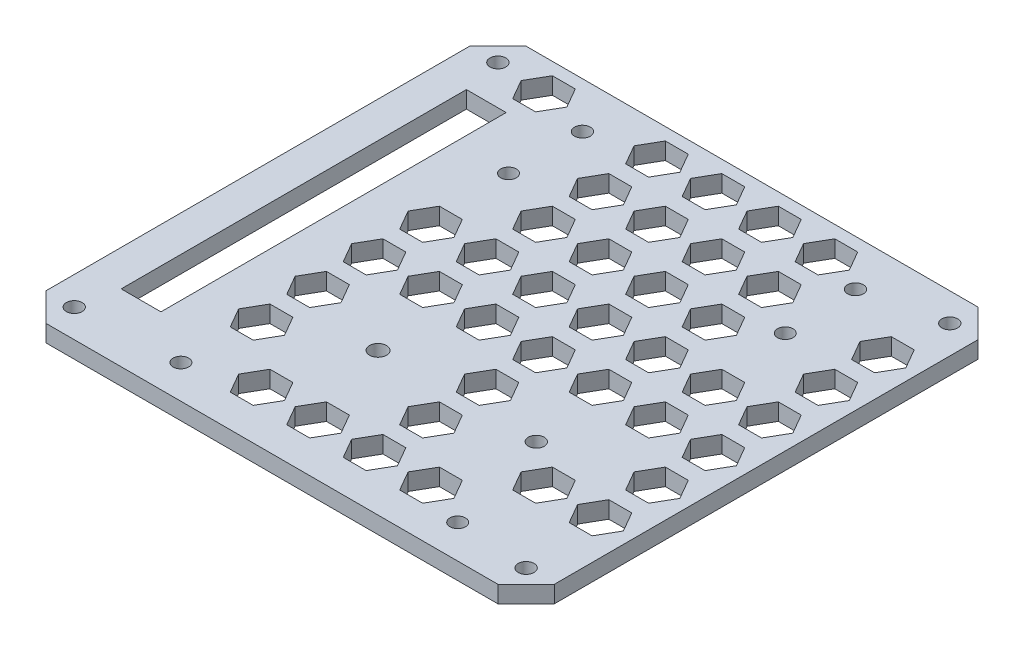
SolidWorks part; units mm, degrees
ref_plane "Front Plane" through (0, 0, 0) normal (0, 0, 1) x (1, 0, 0)
ref_plane "Top Plane" through (0, 0, 0) normal (0, 1, 0) x (1, 0, 0)
ref_plane "Right Plane" through (0, 0, 0) normal (1, 0, 0) x (0, 0, -1)
sketch "Sketch1" plane through (0, 0, 0) normal (0, 1, 0) x (1, 0, 0)
  line L0 (-40, 37.5) -> (40, 37.5) construction
  line L1 (40, 37.5) -> (40, -37.5) construction
  line L2 (40, -37.5) -> (-40, -37.5) construction
  line L3 (-40, -37.5) -> (-40, 37.5) construction
  line L4 (-40, 37.5) -> (-40, 42.5) construction
  line L5 (-40, 37.5) -> (-45, 37.5) construction
  line L6 (40, -37.5) -> (45, -37.5) construction
  line L7 (40, -37.5) -> (40, -42.5) construction
  line L8 (-45, 42.5) -> (-45, -42.5)
  line L9 (-45, -42.5) -> (45, -42.5)
  line L10 (45, -42.5) -> (45, 42.5)
  line L11 (45, 42.5) -> (-45, 42.5)
  circle A0 centre (-40, 37.5) radius 1.4
  circle A1 centre (40, 37.5) radius 1.4
  circle A2 centre (40, -37.5) radius 1.4
  circle A3 centre (-40, -37.5) radius 1.4
extrude "Boss-Extrude1" add sketch "Sketch1" along normal blind 3
sketch "Sketch4" plane through (0, 3, 0) normal (0, 1, 0) x (1, 0, 0)
  circle A0 centre (26.9483, -36.5641) radius 1.375
  circle A1 centre (-22.0517, -36.5641) radius 1.375
  circle A2 centre (-22.0517, 21.4359) radius 1.375
  circle A3 centre (26.9483, 21.4359) radius 1.375
extrude "Cut-Extrude1" cut sketch "Sketch4" against normal blind 10
sketch "Sketch5" plane through (0, 0, 0) normal (0, -1, 0) x (-1, 0, 0)
  circle A0 centre (6.4695, -17.2479) radius 1.5
  circle A1 centre (-21.5467, -17.2479) radius 1.4
  circle A2 centre (-26.4252, 34.3776) radius 1.4
  circle A3 centre (21.911, 34.3776) radius 1.4
extrude "Cut-Extrude2" cut sketch "Sketch5" against normal blind 10 contours A3 | A2 | A0 | A1
sketch "Sketch6" plane through (0, 3, 0) normal (0, 1, 0) x (1, 0, 0)
  line L1 (-31.5917, -30.5577) -> (-38.6326, -30.5577)
  line L2 (-31.5917, -30.5577) -> (-31.5917, 30.5577)
  line L3 (-31.5917, 30.5577) -> (-38.6326, 30.5577)
  line L4 (-38.6326, -30.5577) -> (-38.6326, 30.5577)
  line L5 (-31.5917, -30.5577) -> (-38.6326, 30.5577) construction
  line L6 (-31.5917, 30.5577) -> (-38.6326, -30.5577) construction
  point P0 (-35.1122, 0)
extrude "Cut-Extrude3" cut sketch "Sketch6" against normal blind 10
chamfer "Chamfer1" distance 5 angle 45 4 edges at (-45, 1.5, 42.5) (45, 1.5, 42.5) (45, 1.5, -42.5) (-45, 1.5, -42.5)
sketch "Sketch7" plane through (0, 3, 0) normal (0, 1, 0) x (1, 0, 0)
  line L0 (40, 42.5) -> (-40, 42.5) construction
  line L1 (-29.0872, 33.2663) -> (-27.0592, 36.7789)
  line L2 (-27.0592, 36.7789) -> (-29.0872, 40.2914)
  line L3 (-29.0872, 40.2914) -> (-33.1431, 40.2914)
  line L4 (-33.1431, 40.2914) -> (-35.1711, 36.7789)
  line L5 (-35.1711, 36.7789) -> (-33.1431, 33.2663)
  line L6 (-33.1431, 33.2663) -> (-29.0872, 33.2663)
  line L7 (-19.0872, 33.2663) -> (-17.0592, 36.7789) [skipped]
  line L8 (-17.0592, 36.7789) -> (-19.0872, 40.2914) [skipped]
  line L9 (-19.0872, 40.2914) -> (-23.1431, 40.2914) [skipped]
  line L10 (-23.1431, 40.2914) -> (-25.1711, 36.7789) [skipped]
  line L11 (-25.1711, 36.7789) -> (-23.1431, 33.2663) [skipped]
  line L12 (-23.1431, 33.2663) -> (-19.0872, 33.2663) [skipped]
  line L13 (-9.0872, 33.2663) -> (-7.0592, 36.7789)
  line L14 (-7.0592, 36.7789) -> (-9.0872, 40.2914)
  line L15 (-9.0872, 40.2914) -> (-13.1431, 40.2914)
  line L16 (-13.1431, 40.2914) -> (-15.1711, 36.7789)
  line L17 (-15.1711, 36.7789) -> (-13.1431, 33.2663)
  line L18 (-13.1431, 33.2663) -> (-9.0872, 33.2663)
  line L19 (0.9128, 33.2663) -> (2.9408, 36.7789)
  line L20 (2.9408, 36.7789) -> (0.9128, 40.2914)
  line L21 (0.9128, 40.2914) -> (-3.1431, 40.2914)
  line L22 (-3.1431, 40.2914) -> (-5.1711, 36.7789)
  line L23 (-5.1711, 36.7789) -> (-3.1431, 33.2663)
  line L24 (-3.1431, 33.2663) -> (0.9128, 33.2663)
  line L25 (10.9128, 33.2663) -> (12.9408, 36.7789)
  line L26 (12.9408, 36.7789) -> (10.9128, 40.2914)
  line L27 (10.9128, 40.2914) -> (6.8569, 40.2914)
  line L28 (6.8569, 40.2914) -> (4.8289, 36.7789)
  line L29 (4.8289, 36.7789) -> (6.8569, 33.2663)
  line L30 (6.8569, 33.2663) -> (10.9128, 33.2663)
  line L31 (20.9128, 33.2663) -> (22.9408, 36.7789)
  line L32 (22.9408, 36.7789) -> (20.9128, 40.2914)
  line L33 (20.9128, 40.2914) -> (16.8569, 40.2914)
  line L34 (16.8569, 40.2914) -> (14.8289, 36.7789)
  line L35 (14.8289, 36.7789) -> (16.8569, 33.2663)
  line L36 (16.8569, 33.2663) -> (20.9128, 33.2663)
  line L37 (30.9128, 33.2663) -> (32.9408, 36.7789) [skipped]
  line L38 (32.9408, 36.7789) -> (30.9128, 40.2914) [skipped]
  line L39 (30.9128, 40.2914) -> (26.8569, 40.2914) [skipped]
  line L40 (26.8569, 40.2914) -> (24.8289, 36.7789) [skipped]
  line L41 (24.8289, 36.7789) -> (26.8569, 33.2663) [skipped]
  line L42 (26.8569, 33.2663) -> (30.9128, 33.2663) [skipped]
  line L43 (40.9128, 33.2663) -> (42.9408, 36.7789) [skipped]
  line L44 (42.9408, 36.7789) -> (40.9128, 40.2914) [skipped]
  line L45 (40.9128, 40.2914) -> (36.8569, 40.2914) [skipped]
  line L46 (36.8569, 40.2914) -> (34.8289, 36.7789) [skipped]
  line L47 (34.8289, 36.7789) -> (36.8569, 33.2663) [skipped]
  line L48 (36.8569, 33.2663) -> (40.9128, 33.2663) [skipped]
  line L49 (-19.0872, 23.2663) -> (-17.0592, 26.7789) [skipped]
  line L50 (-17.0592, 26.7789) -> (-19.0872, 30.2914) [skipped]
  line L51 (-19.0872, 30.2914) -> (-23.1431, 30.2914) [skipped]
  line L52 (-23.1431, 30.2914) -> (-25.1711, 26.7789) [skipped]
  line L53 (-25.1711, 26.7789) -> (-23.1431, 23.2663) [skipped]
  line L54 (-23.1431, 23.2663) -> (-19.0872, 23.2663) [skipped]
  line L55 (-9.0872, 23.2663) -> (-7.0592, 26.7789)
  line L56 (-7.0592, 26.7789) -> (-9.0872, 30.2914)
  line L57 (-9.0872, 30.2914) -> (-13.1431, 30.2914)
  line L58 (-13.1431, 30.2914) -> (-15.1711, 26.7789)
  line L59 (-15.1711, 26.7789) -> (-13.1431, 23.2663)
  line L60 (-13.1431, 23.2663) -> (-9.0872, 23.2663)
  line L61 (0.9128, 23.2663) -> (2.9408, 26.7789)
  line L62 (2.9408, 26.7789) -> (0.9128, 30.2914)
  line L63 (0.9128, 30.2914) -> (-3.1431, 30.2914)
  line L64 (-3.1431, 30.2914) -> (-5.1711, 26.7789)
  line L65 (-5.1711, 26.7789) -> (-3.1431, 23.2663)
  line L66 (-3.1431, 23.2663) -> (0.9128, 23.2663)
  line L67 (10.9128, 23.2663) -> (12.9408, 26.7789)
  line L68 (12.9408, 26.7789) -> (10.9128, 30.2914)
  line L69 (10.9128, 30.2914) -> (6.8569, 30.2914)
  line L70 (6.8569, 30.2914) -> (4.8289, 26.7789)
  line L71 (4.8289, 26.7789) -> (6.8569, 23.2663)
  line L72 (6.8569, 23.2663) -> (10.9128, 23.2663)
  line L73 (20.9128, 23.2663) -> (22.9408, 26.7789)
  line L74 (22.9408, 26.7789) -> (20.9128, 30.2914)
  line L75 (20.9128, 30.2914) -> (16.8569, 30.2914)
  line L76 (16.8569, 30.2914) -> (14.8289, 26.7789)
  line L77 (14.8289, 26.7789) -> (16.8569, 23.2663)
  line L78 (16.8569, 23.2663) -> (20.9128, 23.2663)
  line L79 (30.9128, 23.2663) -> (32.9408, 26.7789) [skipped]
  line L80 (32.9408, 26.7789) -> (30.9128, 30.2914) [skipped]
  line L81 (30.9128, 30.2914) -> (26.8569, 30.2914) [skipped]
  line L82 (26.8569, 30.2914) -> (24.8289, 26.7789) [skipped]
  line L83 (24.8289, 26.7789) -> (26.8569, 23.2663) [skipped]
  line L84 (26.8569, 23.2663) -> (30.9128, 23.2663) [skipped]
  line L85 (40.9128, 23.2663) -> (42.9408, 26.7789)
  line L86 (42.9408, 26.7789) -> (40.9128, 30.2914)
  line L87 (40.9128, 30.2914) -> (36.8569, 30.2914)
  line L88 (36.8569, 30.2914) -> (34.8289, 26.7789)
  line L89 (34.8289, 26.7789) -> (36.8569, 23.2663)
  line L90 (36.8569, 23.2663) -> (40.9128, 23.2663)
  line L91 (-19.0872, 13.2663) -> (-17.0592, 16.7789) [skipped]
  line L92 (-17.0592, 16.7789) -> (-19.0872, 20.2914) [skipped]
  line L93 (-19.0872, 20.2914) -> (-23.1431, 20.2914) [skipped]
  line L94 (-23.1431, 20.2914) -> (-25.1711, 16.7789) [skipped]
  line L95 (-25.1711, 16.7789) -> (-23.1431, 13.2663) [skipped]
  line L96 (-23.1431, 13.2663) -> (-19.0872, 13.2663) [skipped]
  line L97 (-9.0872, 13.2663) -> (-7.0592, 16.7789)
  line L98 (-7.0592, 16.7789) -> (-9.0872, 20.2914)
  line L99 (-9.0872, 20.2914) -> (-13.1431, 20.2914)
  line L100 (-13.1431, 20.2914) -> (-15.1711, 16.7789)
  line L101 (-15.1711, 16.7789) -> (-13.1431, 13.2663)
  line L102 (-13.1431, 13.2663) -> (-9.0872, 13.2663)
  line L103 (0.9128, 13.2663) -> (2.9408, 16.7789)
  line L104 (2.9408, 16.7789) -> (0.9128, 20.2914)
  line L105 (0.9128, 20.2914) -> (-3.1431, 20.2914)
  line L106 (-3.1431, 20.2914) -> (-5.1711, 16.7789)
  line L107 (-5.1711, 16.7789) -> (-3.1431, 13.2663)
  line L108 (-3.1431, 13.2663) -> (0.9128, 13.2663)
  line L109 (10.9128, 13.2663) -> (12.9408, 16.7789)
  line L110 (12.9408, 16.7789) -> (10.9128, 20.2914)
  line L111 (10.9128, 20.2914) -> (6.8569, 20.2914)
  line L112 (6.8569, 20.2914) -> (4.8289, 16.7789)
  line L113 (4.8289, 16.7789) -> (6.8569, 13.2663)
  line L114 (6.8569, 13.2663) -> (10.9128, 13.2663)
  line L115 (20.9128, 13.2663) -> (22.9408, 16.7789)
  line L116 (22.9408, 16.7789) -> (20.9128, 20.2914)
  line L117 (20.9128, 20.2914) -> (16.8569, 20.2914)
  line L118 (16.8569, 20.2914) -> (14.8289, 16.7789)
  line L119 (14.8289, 16.7789) -> (16.8569, 13.2663)
  line L120 (16.8569, 13.2663) -> (20.9128, 13.2663)
  line L121 (30.9128, 13.2663) -> (32.9408, 16.7789) [skipped]
  line L122 (32.9408, 16.7789) -> (30.9128, 20.2914) [skipped]
  line L123 (30.9128, 20.2914) -> (26.8569, 20.2914) [skipped]
  line L124 (26.8569, 20.2914) -> (24.8289, 16.7789) [skipped]
  line L125 (24.8289, 16.7789) -> (26.8569, 13.2663) [skipped]
  line L126 (26.8569, 13.2663) -> (30.9128, 13.2663) [skipped]
  line L127 (40.9128, 13.2663) -> (42.9408, 16.7789)
  line L128 (42.9408, 16.7789) -> (40.9128, 20.2914)
  line L129 (40.9128, 20.2914) -> (36.8569, 20.2914)
  line L130 (36.8569, 20.2914) -> (34.8289, 16.7789)
  line L131 (34.8289, 16.7789) -> (36.8569, 13.2663)
  line L132 (36.8569, 13.2663) -> (40.9128, 13.2663)
  line L133 (-19.0872, 3.2663) -> (-17.0592, 6.7789)
  line L134 (-17.0592, 6.7789) -> (-19.0872, 10.2914)
  line L135 (-19.0872, 10.2914) -> (-23.1431, 10.2914)
  line L136 (-23.1431, 10.2914) -> (-25.1711, 6.7789)
  line L137 (-25.1711, 6.7789) -> (-23.1431, 3.2663)
  line L138 (-23.1431, 3.2663) -> (-19.0872, 3.2663)
  line L139 (-9.0872, 3.2663) -> (-7.0592, 6.7789)
  line L140 (-7.0592, 6.7789) -> (-9.0872, 10.2914)
  line L141 (-9.0872, 10.2914) -> (-13.1431, 10.2914)
  line L142 (-13.1431, 10.2914) -> (-15.1711, 6.7789)
  line L143 (-15.1711, 6.7789) -> (-13.1431, 3.2663)
  line L144 (-13.1431, 3.2663) -> (-9.0872, 3.2663)
  line L145 (0.9128, 3.2663) -> (2.9408, 6.7789)
  line L146 (2.9408, 6.7789) -> (0.9128, 10.2914)
  line L147 (0.9128, 10.2914) -> (-3.1431, 10.2914)
  line L148 (-3.1431, 10.2914) -> (-5.1711, 6.7789)
  line L149 (-5.1711, 6.7789) -> (-3.1431, 3.2663)
  line L150 (-3.1431, 3.2663) -> (0.9128, 3.2663)
  line L151 (10.9128, 3.2663) -> (12.9408, 6.7789)
  line L152 (12.9408, 6.7789) -> (10.9128, 10.2914)
  line L153 (10.9128, 10.2914) -> (6.8569, 10.2914)
  line L154 (6.8569, 10.2914) -> (4.8289, 6.7789)
  line L155 (4.8289, 6.7789) -> (6.8569, 3.2663)
  line L156 (6.8569, 3.2663) -> (10.9128, 3.2663)
  line L157 (20.9128, 3.2663) -> (22.9408, 6.7789)
  line L158 (22.9408, 6.7789) -> (20.9128, 10.2914)
  line L159 (20.9128, 10.2914) -> (16.8569, 10.2914)
  line L160 (16.8569, 10.2914) -> (14.8289, 6.7789)
  line L161 (14.8289, 6.7789) -> (16.8569, 3.2663)
  line L162 (16.8569, 3.2663) -> (20.9128, 3.2663)
  line L163 (30.9128, 3.2663) -> (32.9408, 6.7789)
  line L164 (32.9408, 6.7789) -> (30.9128, 10.2914)
  line L165 (30.9128, 10.2914) -> (26.8569, 10.2914)
  line L166 (26.8569, 10.2914) -> (24.8289, 6.7789)
  line L167 (24.8289, 6.7789) -> (26.8569, 3.2663)
  line L168 (26.8569, 3.2663) -> (30.9128, 3.2663)
  line L169 (40.9128, 3.2663) -> (42.9408, 6.7789)
  line L170 (42.9408, 6.7789) -> (40.9128, 10.2914)
  line L171 (40.9128, 10.2914) -> (36.8569, 10.2914)
  line L172 (36.8569, 10.2914) -> (34.8289, 6.7789)
  line L173 (34.8289, 6.7789) -> (36.8569, 3.2663)
  line L174 (36.8569, 3.2663) -> (40.9128, 3.2663)
  line L175 (-19.0872, -6.7337) -> (-17.0592, -3.2211)
  line L176 (-17.0592, -3.2211) -> (-19.0872, 0.2914)
  line L177 (-19.0872, 0.2914) -> (-23.1431, 0.2914)
  line L178 (-23.1431, 0.2914) -> (-25.1711, -3.2211)
  line L179 (-25.1711, -3.2211) -> (-23.1431, -6.7337)
  line L180 (-23.1431, -6.7337) -> (-19.0872, -6.7337)
  line L181 (-9.0872, -6.7337) -> (-7.0592, -3.2211)
  line L182 (-7.0592, -3.2211) -> (-9.0872, 0.2914)
  line L183 (-9.0872, 0.2914) -> (-13.1431, 0.2914)
  line L184 (-13.1431, 0.2914) -> (-15.1711, -3.2211)
  line L185 (-15.1711, -3.2211) -> (-13.1431, -6.7337)
  line L186 (-13.1431, -6.7337) -> (-9.0872, -6.7337)
  line L187 (0.9128, -6.7337) -> (2.9408, -3.2211)
  line L188 (2.9408, -3.2211) -> (0.9128, 0.2914)
  line L189 (0.9128, 0.2914) -> (-3.1431, 0.2914)
  line L190 (-3.1431, 0.2914) -> (-5.1711, -3.2211)
  line L191 (-5.1711, -3.2211) -> (-3.1431, -6.7337)
  line L192 (-3.1431, -6.7337) -> (0.9128, -6.7337)
  line L193 (10.9128, -6.7337) -> (12.9408, -3.2211)
  line L194 (12.9408, -3.2211) -> (10.9128, 0.2914)
  line L195 (10.9128, 0.2914) -> (6.8569, 0.2914)
  line L196 (6.8569, 0.2914) -> (4.8289, -3.2211)
  line L197 (4.8289, -3.2211) -> (6.8569, -6.7337)
  line L198 (6.8569, -6.7337) -> (10.9128, -6.7337)
  line L199 (20.9128, -6.7337) -> (22.9408, -3.2211)
  line L200 (22.9408, -3.2211) -> (20.9128, 0.2914)
  line L201 (20.9128, 0.2914) -> (16.8569, 0.2914)
  line L202 (16.8569, 0.2914) -> (14.8289, -3.2211)
  line L203 (14.8289, -3.2211) -> (16.8569, -6.7337)
  line L204 (16.8569, -6.7337) -> (20.9128, -6.7337)
  line L205 (30.9128, -6.7337) -> (32.9408, -3.2211)
  line L206 (32.9408, -3.2211) -> (30.9128, 0.2914)
  line L207 (30.9128, 0.2914) -> (26.8569, 0.2914)
  line L208 (26.8569, 0.2914) -> (24.8289, -3.2211)
  line L209 (24.8289, -3.2211) -> (26.8569, -6.7337)
  line L210 (26.8569, -6.7337) -> (30.9128, -6.7337)
  line L211 (40.9128, -6.7337) -> (42.9408, -3.2211)
  line L212 (42.9408, -3.2211) -> (40.9128, 0.2914)
  line L213 (40.9128, 0.2914) -> (36.8569, 0.2914)
  line L214 (36.8569, 0.2914) -> (34.8289, -3.2211)
  line L215 (34.8289, -3.2211) -> (36.8569, -6.7337)
  line L216 (36.8569, -6.7337) -> (40.9128, -6.7337)
  line L217 (-19.0872, -16.7337) -> (-17.0592, -13.2211)
  line L218 (-17.0592, -13.2211) -> (-19.0872, -9.7086)
  line L219 (-19.0872, -9.7086) -> (-23.1431, -9.7086)
  line L220 (-23.1431, -9.7086) -> (-25.1711, -13.2211)
  line L221 (-25.1711, -13.2211) -> (-23.1431, -16.7337)
  line L222 (-23.1431, -16.7337) -> (-19.0872, -16.7337)
  line L223 (-9.0872, -16.7337) -> (-7.0592, -13.2211) [skipped]
  line L224 (-7.0592, -13.2211) -> (-9.0872, -9.7086) [skipped]
  line L225 (-9.0872, -9.7086) -> (-13.1431, -9.7086) [skipped]
  line L226 (-13.1431, -9.7086) -> (-15.1711, -13.2211) [skipped]
  line L227 (-15.1711, -13.2211) -> (-13.1431, -16.7337) [skipped]
  line L228 (-13.1431, -16.7337) -> (-9.0872, -16.7337) [skipped]
  line L229 (0.9128, -16.7337) -> (2.9408, -13.2211) [skipped]
  line L230 (2.9408, -13.2211) -> (0.9128, -9.7086) [skipped]
  line L231 (0.9128, -9.7086) -> (-3.1431, -9.7086) [skipped]
  line L232 (-3.1431, -9.7086) -> (-5.1711, -13.2211) [skipped]
  line L233 (-5.1711, -13.2211) -> (-3.1431, -16.7337) [skipped]
  line L234 (-3.1431, -16.7337) -> (0.9128, -16.7337) [skipped]
  line L235 (10.9128, -16.7337) -> (12.9408, -13.2211)
  line L236 (12.9408, -13.2211) -> (10.9128, -9.7086)
  line L237 (10.9128, -9.7086) -> (6.8569, -9.7086)
  line L238 (6.8569, -9.7086) -> (4.8289, -13.2211)
  line L239 (4.8289, -13.2211) -> (6.8569, -16.7337)
  line L240 (6.8569, -16.7337) -> (10.9128, -16.7337)
  line L241 (20.9128, -16.7337) -> (22.9408, -13.2211) [skipped]
  line L242 (22.9408, -13.2211) -> (20.9128, -9.7086) [skipped]
  line L243 (20.9128, -9.7086) -> (16.8569, -9.7086) [skipped]
  line L244 (16.8569, -9.7086) -> (14.8289, -13.2211) [skipped]
  line L245 (14.8289, -13.2211) -> (16.8569, -16.7337) [skipped]
  line L246 (16.8569, -16.7337) -> (20.9128, -16.7337) [skipped]
  line L247 (30.9128, -16.7337) -> (32.9408, -13.2211) [skipped]
  line L248 (32.9408, -13.2211) -> (30.9128, -9.7086) [skipped]
  line L249 (30.9128, -9.7086) -> (26.8569, -9.7086) [skipped]
  line L250 (26.8569, -9.7086) -> (24.8289, -13.2211) [skipped]
  line L251 (24.8289, -13.2211) -> (26.8569, -16.7337) [skipped]
  line L252 (26.8569, -16.7337) -> (30.9128, -16.7337) [skipped]
  line L253 (40.9128, -16.7337) -> (42.9408, -13.2211)
  line L254 (42.9408, -13.2211) -> (40.9128, -9.7086)
  line L255 (40.9128, -9.7086) -> (36.8569, -9.7086)
  line L256 (36.8569, -9.7086) -> (34.8289, -13.2211)
  line L257 (34.8289, -13.2211) -> (36.8569, -16.7337)
  line L258 (36.8569, -16.7337) -> (40.9128, -16.7337)
  line L259 (-19.0872, -26.7337) -> (-17.0592, -23.2211)
  line L260 (-17.0592, -23.2211) -> (-19.0872, -19.7086)
  line L261 (-19.0872, -19.7086) -> (-23.1431, -19.7086)
  line L262 (-23.1431, -19.7086) -> (-25.1711, -23.2211)
  line L263 (-25.1711, -23.2211) -> (-23.1431, -26.7337)
  line L264 (-23.1431, -26.7337) -> (-19.0872, -26.7337)
  line L265 (-9.0872, -26.7337) -> (-7.0592, -23.2211) [skipped]
  line L266 (-7.0592, -23.2211) -> (-9.0872, -19.7086) [skipped]
  line L267 (-9.0872, -19.7086) -> (-13.1431, -19.7086) [skipped]
  line L268 (-13.1431, -19.7086) -> (-15.1711, -23.2211) [skipped]
  line L269 (-15.1711, -23.2211) -> (-13.1431, -26.7337) [skipped]
  line L270 (-13.1431, -26.7337) -> (-9.0872, -26.7337) [skipped]
  line L271 (0.9128, -26.7337) -> (2.9408, -23.2211) [skipped]
  line L272 (2.9408, -23.2211) -> (0.9128, -19.7086) [skipped]
  line L273 (0.9128, -19.7086) -> (-3.1431, -19.7086) [skipped]
  line L274 (-3.1431, -19.7086) -> (-5.1711, -23.2211) [skipped]
  line L275 (-5.1711, -23.2211) -> (-3.1431, -26.7337) [skipped]
  line L276 (-3.1431, -26.7337) -> (0.9128, -26.7337) [skipped]
  line L277 (10.9128, -26.7337) -> (12.9408, -23.2211)
  line L278 (12.9408, -23.2211) -> (10.9128, -19.7086)
  line L279 (10.9128, -19.7086) -> (6.8569, -19.7086)
  line L280 (6.8569, -19.7086) -> (4.8289, -23.2211)
  line L281 (4.8289, -23.2211) -> (6.8569, -26.7337)
  line L282 (6.8569, -26.7337) -> (10.9128, -26.7337)
  line L283 (20.9128, -26.7337) -> (22.9408, -23.2211) [skipped]
  line L284 (22.9408, -23.2211) -> (20.9128, -19.7086) [skipped]
  line L285 (20.9128, -19.7086) -> (16.8569, -19.7086) [skipped]
  line L286 (16.8569, -19.7086) -> (14.8289, -23.2211) [skipped]
  line L287 (14.8289, -23.2211) -> (16.8569, -26.7337) [skipped]
  line L288 (16.8569, -26.7337) -> (20.9128, -26.7337) [skipped]
  line L289 (30.9128, -26.7337) -> (32.9408, -23.2211)
  line L290 (32.9408, -23.2211) -> (30.9128, -19.7086)
  line L291 (30.9128, -19.7086) -> (26.8569, -19.7086)
  line L292 (26.8569, -19.7086) -> (24.8289, -23.2211)
  line L293 (24.8289, -23.2211) -> (26.8569, -26.7337)
  line L294 (26.8569, -26.7337) -> (30.9128, -26.7337)
  line L295 (40.9128, -26.7337) -> (42.9408, -23.2211)
  line L296 (42.9408, -23.2211) -> (40.9128, -19.7086)
  line L297 (40.9128, -19.7086) -> (36.8569, -19.7086)
  line L298 (36.8569, -19.7086) -> (34.8289, -23.2211)
  line L299 (34.8289, -23.2211) -> (36.8569, -26.7337)
  line L300 (36.8569, -26.7337) -> (40.9128, -26.7337)
  line L301 (-19.0872, -36.7337) -> (-17.0592, -33.2211) [skipped]
  line L302 (-17.0592, -33.2211) -> (-19.0872, -29.7086) [skipped]
  line L303 (-19.0872, -29.7086) -> (-23.1431, -29.7086) [skipped]
  line L304 (-23.1431, -29.7086) -> (-25.1711, -33.2211) [skipped]
  line L305 (-25.1711, -33.2211) -> (-23.1431, -36.7337) [skipped]
  line L306 (-23.1431, -36.7337) -> (-19.0872, -36.7337) [skipped]
  line L307 (-9.0872, -36.7337) -> (-7.0592, -33.2211)
  line L308 (-7.0592, -33.2211) -> (-9.0872, -29.7086)
  line L309 (-9.0872, -29.7086) -> (-13.1431, -29.7086)
  line L310 (-13.1431, -29.7086) -> (-15.1711, -33.2211)
  line L311 (-15.1711, -33.2211) -> (-13.1431, -36.7337)
  line L312 (-13.1431, -36.7337) -> (-9.0872, -36.7337)
  line L313 (0.9128, -36.7337) -> (2.9408, -33.2211)
  line L314 (2.9408, -33.2211) -> (0.9128, -29.7086)
  line L315 (0.9128, -29.7086) -> (-3.1431, -29.7086)
  line L316 (-3.1431, -29.7086) -> (-5.1711, -33.2211)
  line L317 (-5.1711, -33.2211) -> (-3.1431, -36.7337)
  line L318 (-3.1431, -36.7337) -> (0.9128, -36.7337)
  line L319 (10.9128, -36.7337) -> (12.9408, -33.2211)
  line L320 (12.9408, -33.2211) -> (10.9128, -29.7086)
  line L321 (10.9128, -29.7086) -> (6.8569, -29.7086)
  line L322 (6.8569, -29.7086) -> (4.8289, -33.2211)
  line L323 (4.8289, -33.2211) -> (6.8569, -36.7337)
  line L324 (6.8569, -36.7337) -> (10.9128, -36.7337)
  line L325 (20.9128, -36.7337) -> (22.9408, -33.2211)
  line L326 (22.9408, -33.2211) -> (20.9128, -29.7086)
  line L327 (20.9128, -29.7086) -> (16.8569, -29.7086)
  line L328 (16.8569, -29.7086) -> (14.8289, -33.2211)
  line L329 (14.8289, -33.2211) -> (16.8569, -36.7337)
  line L330 (16.8569, -36.7337) -> (20.9128, -36.7337)
  line L331 (30.9128, -36.7337) -> (32.9408, -33.2211) [skipped]
  line L332 (32.9408, -33.2211) -> (30.9128, -29.7086) [skipped]
  line L333 (30.9128, -29.7086) -> (26.8569, -29.7086) [skipped]
  line L334 (26.8569, -29.7086) -> (24.8289, -33.2211) [skipped]
  line L335 (24.8289, -33.2211) -> (26.8569, -36.7337) [skipped]
  line L336 (26.8569, -36.7337) -> (30.9128, -36.7337) [skipped]
  line L337 (40.9128, -36.7337) -> (42.9408, -33.2211) [skipped]
  line L338 (42.9408, -33.2211) -> (40.9128, -29.7086) [skipped]
  line L339 (40.9128, -29.7086) -> (36.8569, -29.7086) [skipped]
  line L340 (36.8569, -29.7086) -> (34.8289, -33.2211) [skipped]
  line L341 (34.8289, -33.2211) -> (36.8569, -36.7337) [skipped]
  line L342 (36.8569, -36.7337) -> (40.9128, -36.7337) [skipped]
  line L343 (-29.0872, 23.2663) -> (-27.0592, 26.7789) [skipped]
  line L344 (-27.0592, 26.7789) -> (-29.0872, 30.2914) [skipped]
  line L345 (-29.0872, 30.2914) -> (-33.1431, 30.2914) [skipped]
  line L346 (-33.1431, 30.2914) -> (-35.1711, 26.7789) [skipped]
  line L347 (-35.1711, 26.7789) -> (-33.1431, 23.2663) [skipped]
  line L348 (-33.1431, 23.2663) -> (-29.0872, 23.2663) [skipped]
  line L349 (-29.0872, 13.2663) -> (-27.0592, 16.7789) [skipped]
  line L350 (-27.0592, 16.7789) -> (-29.0872, 20.2914) [skipped]
  line L351 (-29.0872, 20.2914) -> (-33.1431, 20.2914) [skipped]
  line L352 (-33.1431, 20.2914) -> (-35.1711, 16.7789) [skipped]
  line L353 (-35.1711, 16.7789) -> (-33.1431, 13.2663) [skipped]
  line L354 (-33.1431, 13.2663) -> (-29.0872, 13.2663) [skipped]
  line L355 (-29.0872, 3.2663) -> (-27.0592, 6.7789) [skipped]
  line L356 (-27.0592, 6.7789) -> (-29.0872, 10.2914) [skipped]
  line L357 (-29.0872, 10.2914) -> (-33.1431, 10.2914) [skipped]
  line L358 (-33.1431, 10.2914) -> (-35.1711, 6.7789) [skipped]
  line L359 (-35.1711, 6.7789) -> (-33.1431, 3.2663) [skipped]
  line L360 (-33.1431, 3.2663) -> (-29.0872, 3.2663) [skipped]
  line L361 (-29.0872, -6.7337) -> (-27.0592, -3.2211) [skipped]
  line L362 (-27.0592, -3.2211) -> (-29.0872, 0.2914) [skipped]
  line L363 (-29.0872, 0.2914) -> (-33.1431, 0.2914) [skipped]
  line L364 (-33.1431, 0.2914) -> (-35.1711, -3.2211) [skipped]
  line L365 (-35.1711, -3.2211) -> (-33.1431, -6.7337) [skipped]
  line L366 (-33.1431, -6.7337) -> (-29.0872, -6.7337) [skipped]
  line L367 (-29.0872, -16.7337) -> (-27.0592, -13.2211) [skipped]
  line L368 (-27.0592, -13.2211) -> (-29.0872, -9.7086) [skipped]
  line L369 (-29.0872, -9.7086) -> (-33.1431, -9.7086) [skipped]
  line L370 (-33.1431, -9.7086) -> (-35.1711, -13.2211) [skipped]
  line L371 (-35.1711, -13.2211) -> (-33.1431, -16.7337) [skipped]
  line L372 (-33.1431, -16.7337) -> (-29.0872, -16.7337) [skipped]
  line L373 (-29.0872, -26.7337) -> (-27.0592, -23.2211) [skipped]
  line L374 (-27.0592, -23.2211) -> (-29.0872, -19.7086) [skipped]
  line L375 (-29.0872, -19.7086) -> (-33.1431, -19.7086) [skipped]
  line L376 (-33.1431, -19.7086) -> (-35.1711, -23.2211) [skipped]
  line L377 (-35.1711, -23.2211) -> (-33.1431, -26.7337) [skipped]
  line L378 (-33.1431, -26.7337) -> (-29.0872, -26.7337) [skipped]
  line L379 (-29.0872, -36.7337) -> (-27.0592, -33.2211) [skipped]
  line L380 (-27.0592, -33.2211) -> (-29.0872, -29.7086) [skipped]
  line L381 (-29.0872, -29.7086) -> (-33.1431, -29.7086) [skipped]
  line L382 (-33.1431, -29.7086) -> (-35.1711, -33.2211) [skipped]
  line L383 (-35.1711, -33.2211) -> (-33.1431, -36.7337) [skipped]
  line L384 (-33.1431, -36.7337) -> (-29.0872, -36.7337) [skipped]
  circle A0 centre (-31.1151, 36.7789) radius 3.5125 construction
  circle A1 centre (-21.1151, 36.7789) radius 3.5125 construction
  circle A2 centre (-11.1151, 36.7789) radius 3.5125 construction
  circle A3 centre (-1.1151, 36.7789) radius 3.5125 construction
  circle A4 centre (8.8849, 36.7789) radius 3.5125 construction
  circle A5 centre (18.8849, 36.7789) radius 3.5125 construction
  circle A6 centre (28.8849, 36.7789) radius 3.5125 construction
  circle A7 centre (38.8849, 36.7789) radius 3.5125 construction
  circle A8 centre (-21.1151, 26.7789) radius 3.5125 construction
  circle A9 centre (-11.1151, 26.7789) radius 3.5125 construction
  circle A10 centre (-1.1151, 26.7789) radius 3.5125 construction
  circle A11 centre (8.8849, 26.7789) radius 3.5125 construction
  circle A12 centre (18.8849, 26.7789) radius 3.5125 construction
  circle A13 centre (28.8849, 26.7789) radius 3.5125 construction
  circle A14 centre (38.8849, 26.7789) radius 3.5125 construction
  circle A15 centre (-21.1151, 16.7789) radius 3.5125 construction
  circle A16 centre (-11.1151, 16.7789) radius 3.5125 construction
  circle A17 centre (-1.1151, 16.7789) radius 3.5125 construction
  circle A18 centre (8.8849, 16.7789) radius 3.5125 construction
  circle A19 centre (18.8849, 16.7789) radius 3.5125 construction
  circle A20 centre (28.8849, 16.7789) radius 3.5125 construction
  circle A21 centre (38.8849, 16.7789) radius 3.5125 construction
  circle A22 centre (-21.1151, 6.7789) radius 3.5125 construction
  circle A23 centre (-11.1151, 6.7789) radius 3.5125 construction
  circle A24 centre (-1.1151, 6.7789) radius 3.5125 construction
  circle A25 centre (8.8849, 6.7789) radius 3.5125 construction
  circle A26 centre (18.8849, 6.7789) radius 3.5125 construction
  circle A27 centre (28.8849, 6.7789) radius 3.5125 construction
  circle A28 centre (38.8849, 6.7789) radius 3.5125 construction
  circle A29 centre (-21.1151, -3.2211) radius 3.5125 construction
  circle A30 centre (-11.1151, -3.2211) radius 3.5125 construction
  circle A31 centre (-1.1151, -3.2211) radius 3.5125 construction
  circle A32 centre (8.8849, -3.2211) radius 3.5125 construction
  circle A33 centre (18.8849, -3.2211) radius 3.5125 construction
  circle A34 centre (28.8849, -3.2211) radius 3.5125 construction
  circle A35 centre (38.8849, -3.2211) radius 3.5125 construction
  circle A36 centre (-21.1151, -13.2211) radius 3.5125 construction
  circle A37 centre (-11.1151, -13.2211) radius 3.5125 construction
  circle A38 centre (-1.1151, -13.2211) radius 3.5125 construction
  circle A39 centre (8.8849, -13.2211) radius 3.5125 construction
  circle A40 centre (18.8849, -13.2211) radius 3.5125 construction
  circle A41 centre (28.8849, -13.2211) radius 3.5125 construction
  circle A42 centre (38.8849, -13.2211) radius 3.5125 construction
  circle A43 centre (-21.1151, -23.2211) radius 3.5125 construction
  circle A44 centre (-11.1151, -23.2211) radius 3.5125 construction
  circle A45 centre (-1.1151, -23.2211) radius 3.5125 construction
  circle A46 centre (8.8849, -23.2211) radius 3.5125 construction
  circle A47 centre (18.8849, -23.2211) radius 3.5125 construction
  circle A48 centre (28.8849, -23.2211) radius 3.5125 construction
  circle A49 centre (38.8849, -23.2211) radius 3.5125 construction
  circle A50 centre (-21.1151, -33.2211) radius 3.5125 construction
  circle A51 centre (-11.1151, -33.2211) radius 3.5125 construction
  circle A52 centre (-1.1151, -33.2211) radius 3.5125 construction
  circle A53 centre (8.8849, -33.2211) radius 3.5125 construction
  circle A54 centre (18.8849, -33.2211) radius 3.5125 construction
  circle A55 centre (28.8849, -33.2211) radius 3.5125 construction
  circle A56 centre (38.8849, -33.2211) radius 3.5125 construction
  circle A57 centre (-31.1151, 26.7789) radius 3.5125 construction
  circle A58 centre (-31.1151, 16.7789) radius 3.5125 construction
  circle A59 centre (-31.1151, 6.7789) radius 3.5125 construction
  circle A60 centre (-31.1151, -3.2211) radius 3.5125 construction
  circle A61 centre (-31.1151, -13.2211) radius 3.5125 construction
  circle A62 centre (-31.1151, -23.2211) radius 3.5125 construction
  circle A63 centre (-31.1151, -33.2211) radius 3.5125 construction
extrude "Cut-Extrude4" cut sketch "Sketch7" against normal blind 10
